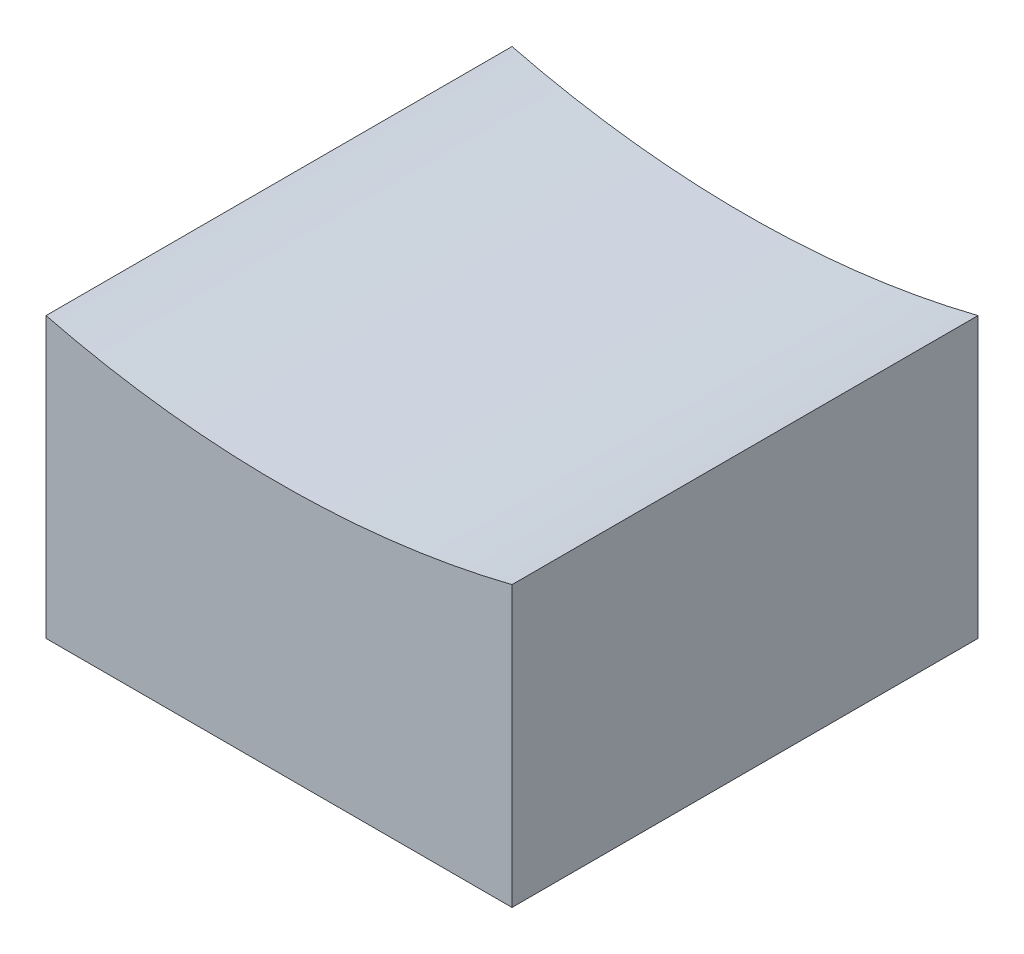
SolidWorks part; units mm, degrees
ref_plane "Front Plane" through (0, 0, 0) normal (0, 0, 1) x (1, 0, 0)
ref_plane "Top Plane" through (0, 0, 0) normal (0, 1, 0) x (1, 0, 0)
ref_plane "Right Plane" through (0, 0, 0) normal (1, 0, 0) x (0, 0, -1)
sketch "Sketch1" plane through (0, 0, 0) normal (0, 0, 1) x (1, 0, 0)
  line L0 (-2.5, 0) -> (2.5, 0)
  line L1 (2.5, 0) -> (2.5, 3)
  line L2 (-2.5, 0) -> (-2.5, 3)
  arc A0 (-2.5, 3) -> (2.5, 3) centre (0, 12.972) ccw
  point P4 (0, 0)
  dimension "D3" = 5
  dimension "D1" = 3
  dimension "D2" = 3
extrude "Boss-Extrude1" add sketch "Sketch1" along normal blind 5
